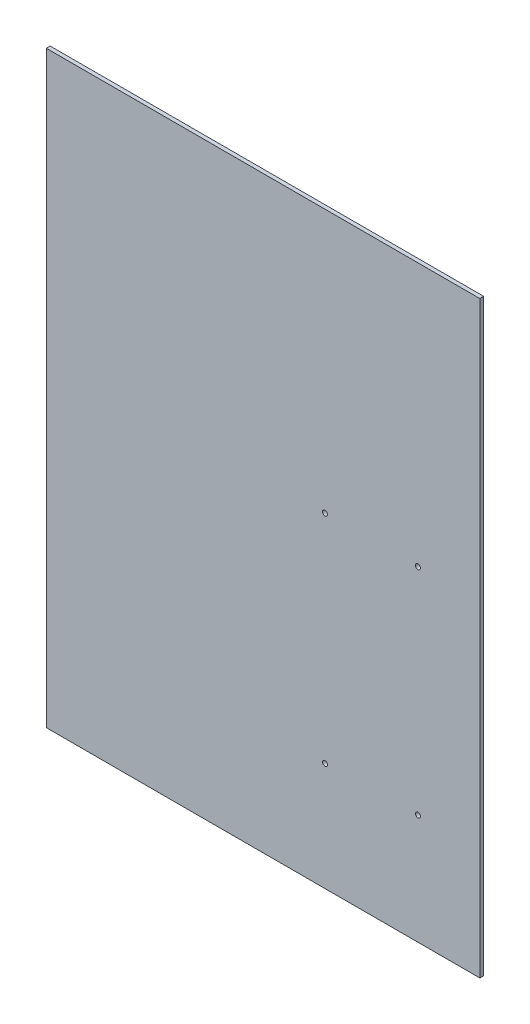
SolidWorks part; units mm, degrees
ref_plane "Front" through (0, 0, 0) normal (0, 0, 1) x (1, 0, 0)
ref_plane "Top" through (0, 0, 0) normal (0, 1, 0) x (1, 0, 0)
ref_plane "Right" through (0, 0, 0) normal (1, 0, 0) x (0, 0, -1)
sketch "Sketch1" plane through (0, 0, 0) normal (0, 0, 1) x (1, 0, 0)
  line L1 (-177.8, 482.6) -> (177.8, 482.6)
  line L2 (-177.8, 482.6) -> (-177.8, 0)
  line L3 (-177.8, 0) -> (177.8, 0)
  line L4 (177.8, 482.6) -> (177.8, 0)
  dimension "D1" = 355.6
  dimension "D2" = 482.6
extrude "Extrude1" add sketch "Sketch1" along normal blind 3.175
hole_wizard "#10 Clearance Hole1" positions "Sketch3" profile "Sketch2" tap size "#10-32" standard "Ansi Inch"
sketch "Sketch3" plane through (0, 0, 0) normal (0, 0, -1) x (-1, 0, 0)
  point P1 (-126.9999, 266.7)
  point P2 (-50.7999, 266.7)
  point P4 (-50.7999, 88.9)
  point P6 (-126.9999, 90.333)
sketch "Sketch2" plane through (126.9999, 266.7, 0) normal (1, 0, 0) x (0, 1, 0)
  line L0 (0, 0) -> (0, 3.175)
  line L1 (0, 3.175) -> (2.0193, 3.175)
  line L2 (2.0193, 3.175) -> (2.0193, 0)
  line L5 (2.0193, 0) -> (0, 0)
  line L11 (0, -6.35) -> (0, 107.95) construction
  dimension "Thru Tap Drill Dia." = 4.0386
  dimension "Thru Tap Drill Depth" = 3.175
cosmetic thread "Cosmetic Thread1" parameters "D1"=3.175, "D2"=4.826
cosmetic thread "Cosmetic Thread2" parameters "D1"=3.175, "D2"=4.826
cosmetic thread "Cosmetic Thread3" parameters "D1"=3.175, "D2"=4.826
cosmetic thread "Cosmetic Thread4" parameters "D1"=3.175, "D2"=4.826
